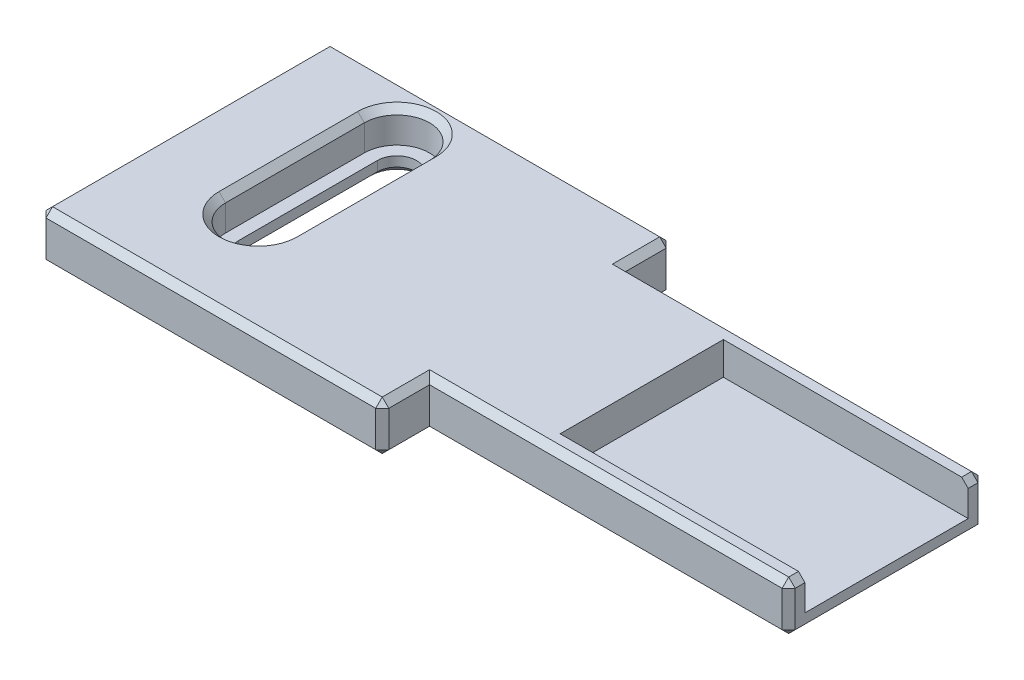
SolidWorks part; units mm, degrees
ref_plane "Front Plane" through (0, 0, 0) normal (0, 0, 1) x (1, 0, 0)
ref_plane "Top Plane" through (0, 0, 0) normal (0, 1, 0) x (1, 0, 0)
ref_plane "Right Plane" through (0, 0, 0) normal (1, 0, 0) x (0, 0, -1)
ref_plane "Plane1" through (0, 38, 0) normal (0, 1, 0) x (1, 0, 0)
sketch "Sketch1" plane through (0, 38, 0) normal (0, 1, 0) x (1, 0, 0)
  line L0 (-28, -2.9) -> (15, -2.9)
  line L1 (15, -2.9) -> (15, 14.9)
  line L2 (15, 14.9) -> (-28, 14.9)
  line L3 (-28, 14.9) -> (-28, -2.9)
extrude "Boss-Extrude1" add sketch "Sketch1" against normal blind 3
sketch "Sketch2" plane through (0, 35, 0) normal (0, -1, 0) x (1, 0, 0)
  line L0 (-7, 2.9) -> (-7, 0)
  line L1 (-7, 0) -> (15, 0)
  line L2 (15, 0) -> (15, 2.9)
  line L3 (15, 2.9) -> (-7, 2.9)
extrude "Cut-Extrude1" cut sketch "Sketch2" against normal through all
sketch "Sketch3" plane through (0, 35, 0) normal (0, -1, 0) x (1, 0, 0)
  line L0 (15, -12) -> (-7, -12)
  line L1 (-7, -12) -> (-7, -14.9)
  line L2 (-7, -14.9) -> (15, -14.9)
  line L3 (15, -14.9) -> (15, -12)
extrude "Cut-Extrude2" cut sketch "Sketch3" against normal through all
sketch "Sketch4" plane through (0, 38, 0) normal (0, 1, 0) x (-1, 0, 0)
  line L0 (22.9, -11.9) -> (22.9, -3.4)
  line L1 (18.9, -3.4) -> (18.9, -11.9)
  arc A0 (22.9, -3.4) -> (18.9, -3.4) centre (20.9, -3.4) ccw
  arc A1 (18.9, -11.9) -> (22.9, -11.9) centre (20.9, -11.9) ccw
extrude "Cut-Extrude3" cut sketch "Sketch4" against normal blind 2
sketch "Sketch5" plane through (0, 35, 0) normal (0, -1, 0) x (1, 0, 0)
  line L0 (-22.1, -3.4) -> (-22.1, -11.9)
  line L1 (-19.7, -11.9) -> (-19.7, -3.4)
  arc A0 (-22.1, -11.9) -> (-19.7, -11.9) centre (-20.9, -11.9) ccw
  arc A1 (-19.7, -3.4) -> (-22.1, -3.4) centre (-20.9, -3.4) ccw
extrude "Cut-Extrude4" cut sketch "Sketch5" against normal through all
sketch "Sketch6" plane through (15, 0, 0) normal (1, 0, 0) x (0, 0, -1)
  line L0 (1, 38) -> (1, 36)
  line L1 (1, 36) -> (11, 36)
  line L2 (11, 36) -> (11, 38)
  line L3 (11, 38) -> (1, 38)
  line L4 (55, 38) -> (-55, 38) construction
  dimension "D1" = 2
extrude "Cut-Extrude5" cut sketch "Sketch6" against normal blind 15
chamfer "Chamfer1" distance 0.4 angle 45 31 edges at (-20.9, 38, -13.9) (-18.9, 38, -7.65) (-22.9, 38, -7.65) (-20.9, 38, -1.4) (-17.5, 35, -14.9) (-7, 35, -13.45) (-7, 36.5, -14.9) (4, 38, -12) (15, 38, -11.5) (15, 36.5, -12) (-7, 38, -13.45) (-28, 35, -6) (-28, 36.5, -14.9) (-17.5, 38, -14.9) (4, 35, -12) (15, 35, -6) (-17.5, 35, 2.9) (-7, 35, 1.45) (-28, 36.5, 2.9) (-28, 38, -6) (4, 35, 0) (-7, 36.5, 2.9) (-17.5, 38, 2.9) (-7, 38, 1.45) (15, 36.5, 0) (4, 38, 0) (15, 38, -0.5) (-20.9, 35, -13.1) (-22.1, 35, -7.65) (-19.7, 35, -7.65) (-20.9, 35, -2.2)
